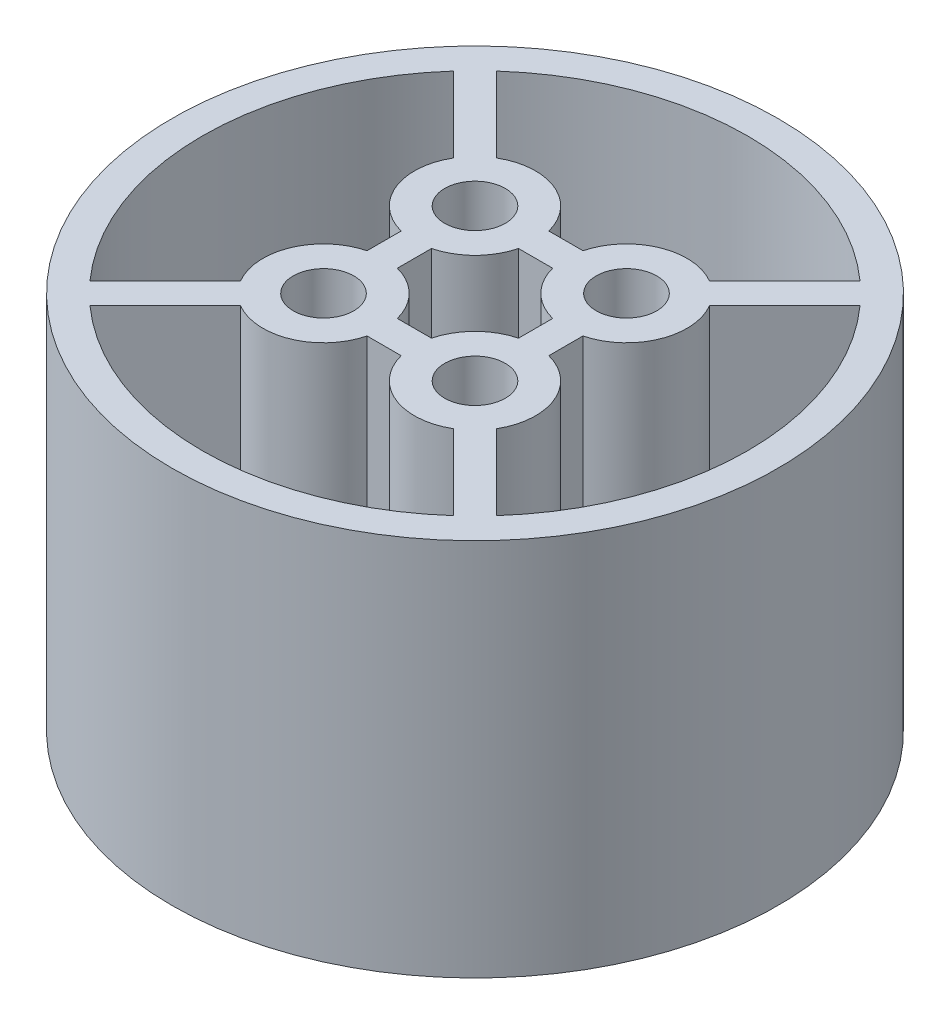
SolidWorks part; units mm, degrees
ref_plane "前视基准面" through (0, 0, 0) normal (0, 0, 1) x (1, 0, 0)
ref_plane "上视基准面" through (0, 0, 0) normal (0, 1, 0) x (1, 0, 0)
ref_plane "右视基准面" through (0, 0, 0) normal (1, 0, 0) x (0, 0, -1)
sketch "草图2" plane through (0, 0, 0) normal (0, 1, 0) x (1, 0, 0)
  line L0 (-20, 0) -> (26.5243, 0) construction
  line L2 (0, -20) -> (0, 31.4697) construction
  line L4 (-8.4457, 7.0315) -> (-13.4154, 12.0012)
  line L5 (-12.0012, 13.4154) -> (-7.0315, 8.4457)
  line L6 (0, 0) -> (-5, 5) construction
  line L7 (7.0315, 8.4457) -> (12.0012, 13.4154)
  line L8 (13.4154, 12.0012) -> (8.4457, 7.0315)
  line L9 (8.4457, -7.0315) -> (13.4154, -12.0012)
  line L10 (12.0012, -13.4154) -> (7.0315, -8.4457)
  line L11 (-7.0315, -8.4457) -> (-12.0012, -13.4154)
  line L12 (-13.4154, -12.0012) -> (-8.4457, -7.0315)
  line L13 (-1.127, 6) -> (1.127, 6)
  line L14 (-1.127, 4) -> (1.127, 4)
  line L17 (-5, 5) -> (5, 5) construction
  line L18 (6, 1.127) -> (6, -1.127)
  line L19 (4, 1.127) -> (4, -1.127)
  line L20 (1.127, -6) -> (-1.127, -6)
  line L21 (1.127, -4) -> (-1.127, -4)
  line L22 (-6, -1.127) -> (-6, 1.127)
  line L23 (-4, -1.127) -> (-4, 1.127)
  arc A1 (-8.4457, 7.0315) -> (-6, 1.127) centre (-5, 5) ccw
  circle A2 centre (0, 0) radius 20
  arc A3 (7.0315, 8.4457) -> (1.127, 6) centre (5, 5) ccw
  arc A4 (8.4457, -7.0315) -> (6, -1.127) centre (5, -5) ccw
  arc A5 (-7.0315, -8.4457) -> (-1.127, -6) centre (-5, -5) ccw
  arc A6 (-13.4154, 12.0012) -> (-13.4154, -12.0012) centre (0, 0) ccw
  arc A7 (-12.0012, -13.4154) -> (12.0012, -13.4154) centre (0, 0) ccw
  arc A8 (13.4154, -12.0012) -> (13.4154, 12.0012) centre (0, 0) ccw
  arc A9 (12.0012, 13.4154) -> (-12.0012, 13.4154) centre (0, 0) ccw
  arc A10 (-4, 1.127) -> (-1.127, 4) centre (-5, 5) ccw
  arc A11 (1.127, 4) -> (4, 1.127) centre (5, 5) ccw
  arc A12 (-6, -1.127) -> (-8.4457, -7.0315) centre (-5, -5) ccw
  arc A13 (1.127, -6) -> (7.0315, -8.4457) centre (5, -5) ccw
  arc A14 (4, -1.127) -> (1.127, -4) centre (5, -5) ccw
  arc A15 (6, 1.127) -> (8.4457, 7.0315) centre (5, 5) ccw
  arc A16 (-1.127, 6) -> (-7.0315, 8.4457) centre (-5, 5) ccw
  arc A17 (-1.127, -4) -> (-4, -1.127) centre (-5, -5) ccw
  circle A18 centre (-5, 5) radius 2
  circle A19 centre (5, 5) radius 2
  circle A20 centre (5, -5) radius 2
  circle A21 centre (-5, -5) radius 2
  point P36 (0, 0)
  point P38 (0, 0)
  point P49 (0, 0)
  point P56 (0, 0)
  dimension "D3" = 4
  dimension "D4" = 8
  dimension "D1" = 40
  dimension "D5" = 36
  dimension "D2" = 5
  dimension "D6" = 2
  dimension "D7" = 4
  dimension "D9" = 2
  dimension "D8" = 4
  dimension "D10" = 4
  dimension "D11" = 4
extrude "凸台-拉伸1" add sketch "草图2" along normal blind 25
